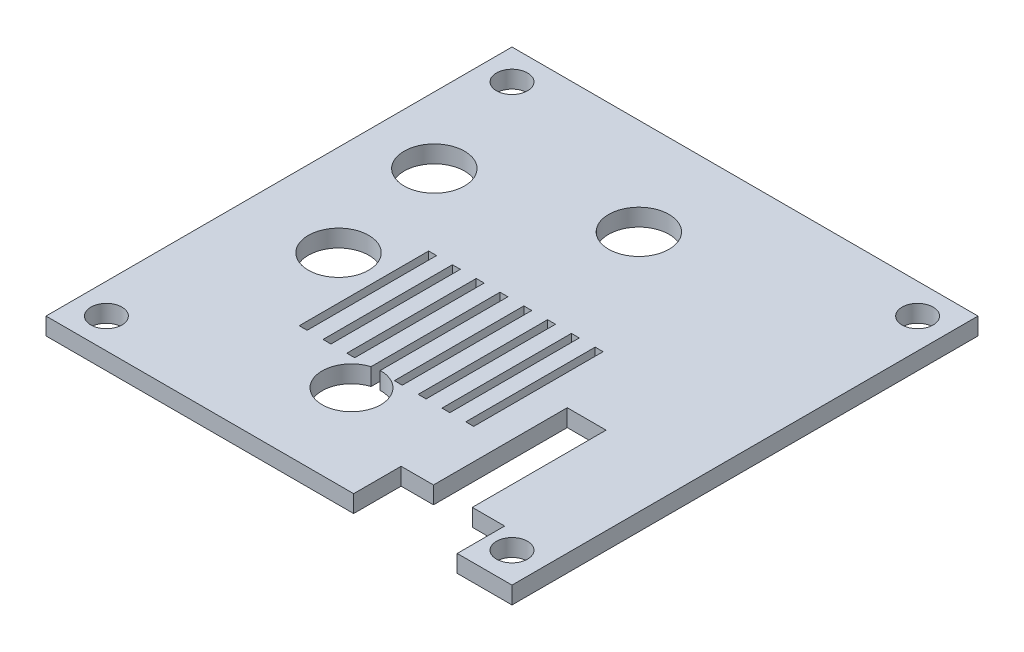
SolidWorks part; units mm, degrees
ref_plane "Front" through (0, 0, 0) normal (0, 0, 1) x (1, 0, 0)
ref_plane "Top" through (0, 0, 0) normal (0, 1, 0) x (1, 0, 0)
ref_plane "Right" through (0, 0, 0) normal (1, 0, 0) x (0, 0, -1)
sketch "草图3" plane through (0, 0, 0) normal (0, 1, 0) x (1, 0, 0)
  line L0 (16.9, -20) -> (20, -20)
  line L1 (-20, -20) -> (12.4, -20)
  line L2 (20, -20) -> (20, 20)
  line L3 (-27, 27) -> (-27, -27)
  line L4 (-27, -27) -> (27, -27)
  line L5 (27, -27) -> (27, 27)
  line L6 (27, 27) -> (-27, 27)
  line L7 (-8.6, 1.7) -> (-7.6812, 1.7)
  line L8 (-5.8437, 1.7) -> (-4.925, 1.7)
  line L9 (20.65, -20) -> (20, -20)
  line L10 (16.9, -6) -> (12.4, -6)
  line L11 (12.4, -6) -> (12.4, -19.5)
  line L12 (-10.4, 20) -> (-4.1, 20)
  line L13 (16.9, -6) -> (16.9, -19.5)
  line L14 (-20, 20) -> (-20, -20)
  line L15 (-3.0875, 1.7) -> (-2.1687, 1.7)
  line L16 (-0.3312, 1.7) -> (0.5875, 1.7)
  line L17 (2.425, 1.7) -> (3.3438, 1.7)
  line L18 (5.1813, 1.7) -> (6.1, 1.7)
  line L19 (8.8563, -13.3) -> (7.9375, -13.3)
  line L20 (8.65, -20) -> (8.65, -27)
  line L21 (-8.6, 1.7) -> (-8.6, -13.3)
  line L22 (-7.6812, -13.3) -> (-8.6, -13.3)
  line L23 (-8.6, -13.3) -> (-8.6029, -13.3589)
  line L24 (-10.4375, -13.3) -> (-11.3562, -13.3)
  line L25 (-10.4375, 1.7) -> (-11.3562, 1.7)
  line L26 (6.1, 1.7) -> (6.1, -13.3)
  line L27 (-4.925, -13.3) -> (-4.925, 1.7)
  line L28 (-11.3562, -13.3) -> (-11.3562, 1.7)
  line L29 (-3.0875, -13.3) -> (-3.0875, 1.7)
  line L30 (-10.4375, -13.3) -> (-10.4375, 1.7)
  line L31 (-2.1687, -13.3) -> (-2.1687, 1.7)
  line L32 (8.8563, 1.7) -> (7.9375, 1.7)
  line L33 (-5.8437, -13.3) -> (-5.8437, 1.7)
  line L34 (8.8563, -13.3) -> (8.8563, 1.7)
  line L35 (-7.6812, -13.3) -> (-7.6812, 1.7)
  line L36 (-0.3312, -13.3) -> (-0.3312, 1.7)
  line L37 (0.5875, -13.3) -> (0.5875, 1.7)
  line L38 (5.1813, -13.3) -> (6.1, -13.3)
  line L39 (2.425, -13.3) -> (2.425, 1.7)
  line L40 (3.3438, -13.3) -> (3.3438, 1.7)
  line L41 (2.425, -13.3) -> (3.3438, -13.3)
  line L42 (5.1813, -13.3) -> (5.1813, 1.7)
  line L43 (-0.3312, -13.3) -> (0.5875, -13.3)
  line L44 (-3.0875, -13.3) -> (-2.1687, -13.3)
  line L45 (-5.8437, -13.3) -> (-4.925, -13.3)
  line L46 (7.9375, -13.3) -> (7.9375, 1.7)
  line L47 (20.65, -20) -> (20.65, -27)
  line L48 (12.4, -19.5) -> (12.4, -20)
  line L49 (16.9, -19.5) -> (16.9, -20)
  line L50 (-20, -20) -> (20, -20) construction
  line L51 (-20, 20) -> (20, 20)
  line L52 (-16.7, 20) -> (-10.4, 20)
  line L53 (20, 20) -> (-20, 20) construction
  line L54 (-16.7, 20) -> (-16.7, 27)
  line L55 (-4.1, 20) -> (-4.1, 27)
  line L56 (12.4, -20) -> (12.4, -21.5)
  line L57 (8.65, -21.5) -> (20.65, -21.5)
  line L58 (16.9, -20) -> (16.9, -21.5)
  circle A0 centre (-23.5, -23.5) radius 1.8
  circle A1 centre (23.5, -23.5) radius 1.8
  circle A2 centre (-23.5, 23.5) radius 1.8
  circle A3 centre (23.5, 23.5) radius 1.8
  circle A4 centre (-2.1, -16.5) radius 2
  circle A5 centre (-16.4, -3.7) radius 2
  circle A6 centre (-19.3, 10.3) radius 2
  circle A7 centre (-1.1, 15.8) radius 2
  circle A8 centre (-19.3, 10.3) radius 3.5
  circle A9 centre (-16.4, -3.7) radius 3.5
  circle A10 centre (-2.1, -16.5) radius 3.4
  circle A11 centre (-1.1, 15.8) radius 3.5
  point P0 (0, 0)
  point P61 (-10.8969, 1.7)
  dimension "D1" = 7
extrude "凸台-拉伸2" add sketch "草图3" along normal blind 2
